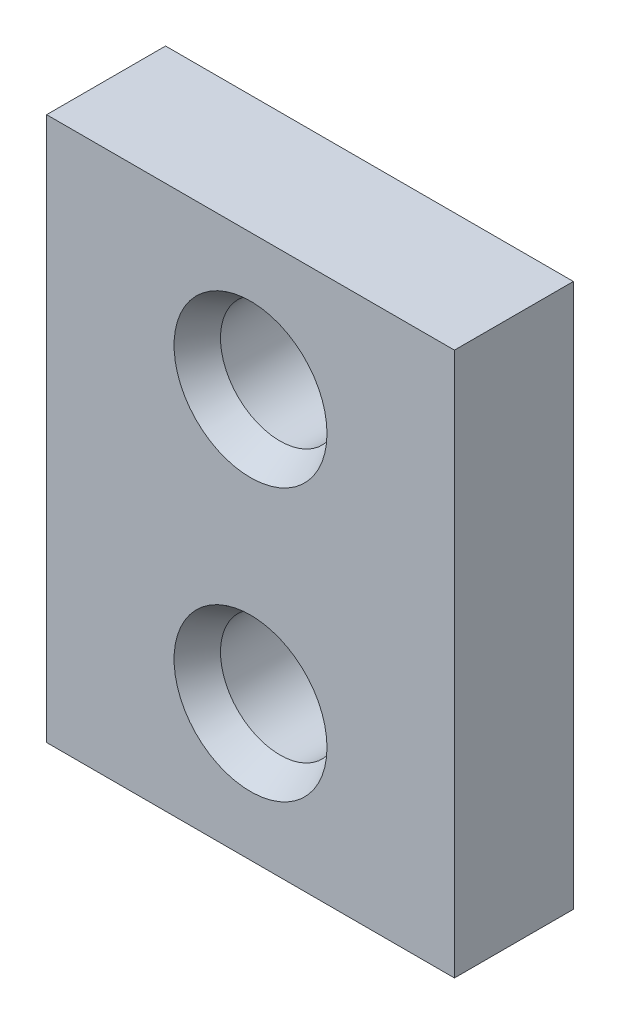
SolidWorks part; units mm, degrees
ref_plane "Front Plane" through (0, 0, 0) normal (0, 0, 1) x (1, 0, 0)
ref_plane "Top Plane" through (0, 0, 0) normal (0, 1, 0) x (1, 0, 0)
ref_plane "Right Plane" through (0, 0, 0) normal (1, 0, 0) x (0, 0, -1)
sketch "Sketch1" plane through (0, 0, 0) normal (0, 0, 1) x (1, 0, 0)
  line L1 (-12, -16) -> (12, -16)
  line L2 (-12, -16) -> (-12, 16)
  line L3 (-12, 16) -> (12, 16)
  line L4 (12, -16) -> (12, 16)
  line L5 (-12, -16) -> (12, 16) construction
  line L6 (-12, 16) -> (12, -16) construction
  point P0 (0, 0)
  dimension "D1" = 24
  dimension "D2" = 32
extrude "Boss-Extrude1" add sketch "Sketch1" along normal mid plane 7
hole_wizard "Hole1" positions "Sketch2" profile "Sketch3" legacy
sketch "Sketch2" plane through (0, 0, 3.5) normal (0, 0, 1) x (1, 0, 0)
  line L0 (12, 16) -> (-12, 16) construction
  point P0 (0, 8)
  point P2 (0, -8)
  dimension "D1" = 8
  dimension "D2" = 16
sketch "Sketch3" plane through (0, 8, 3.5) normal (1, 0, 0) x (0, -1, 0)
  line L0 (0, 0) -> (0, 12)
  line L1 (0, 12) -> (3.5, 12)
  line L2 (3.5, 12) -> (3.5, 1.7321)
  line L3 (3.5, 1.7321) -> (4.5, 0)
  line L4 (4.5, 0) -> (0, 0)
  line L5 (0, -6.4453) -> (0, 115.525) construction
  line L6 (-3.5, 1.7321) -> (-4.5, 0) construction
  dimension "Diameter" = 7
  dimension "Depth" = 12
  dimension "C-Sink Angle" = 60
  dimension "C-Sink Diameter" = 9
